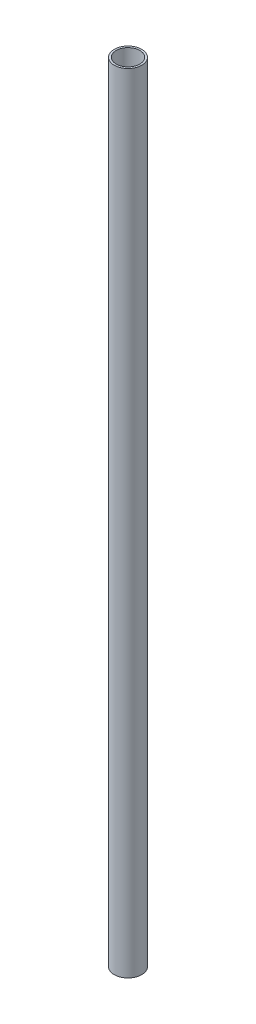
SolidWorks part; units mm, degrees
material "Сплав 2024"
ref_plane "Front" through (0, 0, 0) normal (0, 0, 1) x (1, 0, 0)
ref_plane "Top" through (0, 0, 0) normal (0, 1, 0) x (1, 0, 0)
ref_plane "Right" through (0, 0, 0) normal (1, 0, 0) x (0, 0, -1)
sketch "Эскиз1" plane through (0, 0, 0) normal (0, 1, 0) x (1, 0, 0)
  circle A0 centre (0, 0) radius 7
  circle A1 centre (0, 0) radius 6
  dimension "D1" = 14
  dimension "D2" = 12
extrude "Бобышка-Вытянуть1" add sketch "Эскиз1" along normal blind 400
